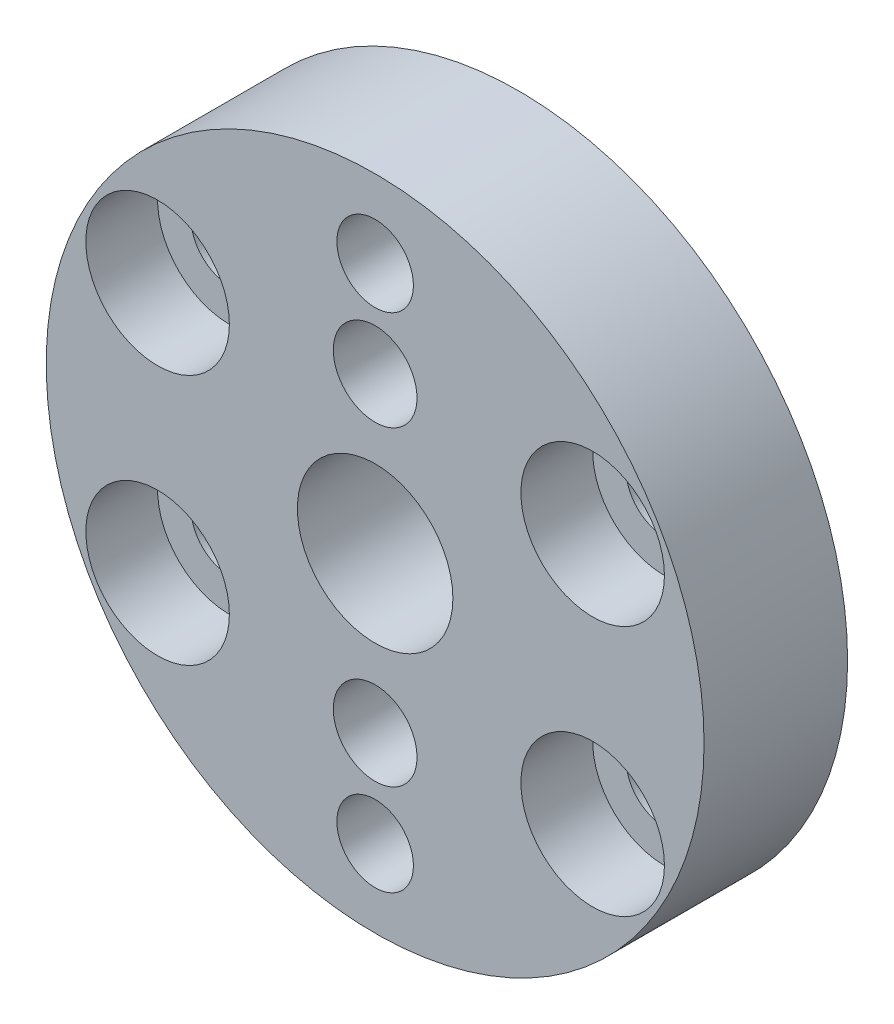
SolidWorks part; units mm, degrees
ref_plane "正面" through (0, 0, 0) normal (0, 0, 1) x (1, 0, 0)
ref_plane "平面" through (0, 0, 0) normal (0, 1, 0) x (1, 0, 0)
ref_plane "右側面" through (0, 0, 0) normal (1, 0, 0) x (0, 0, -1)
sketch "ｽｹｯﾁ1" plane through (0, 0, 0) normal (0, 0, 1) x (1, 0, 0)
  circle A0 centre (0, 0) radius 13.75
  circle A1 centre (0, 0) radius 10.5 construction
  circle A2 centre (0, 10.5) radius 1.6
  circle A3 centre (9.0933, 5.25) radius 1.6
  circle A4 centre (9.0933, -5.25) radius 1.6
  circle A5 centre (0, -10.5) radius 1.6
  circle A6 centre (-9.0933, -5.25) radius 1.6
  circle A7 centre (-9.0933, 5.25) radius 1.6
  circle A8 centre (0, 0) radius 3.25
  point P18 (0, 0)
  dimension "D1" = 27.5
  dimension "D2" = 21
  dimension "D3" = 3.2
  dimension "D5" = 6.5
  dimension "D4" = 6
extrude "ﾎﾞｽ - 押し出し1" add sketch "ｽｹｯﾁ1" along normal blind 6
sketch "ｽｹｯﾁ2" plane through (0, 0, 6) normal (0, 0, 1) x (1, 0, 0)
  line L0 (0, 10.5) -> (0, 0) construction
  line L1 (0, 0) -> (0, 6.5) construction
  circle A0 centre (0, 0) radius 6.5 construction
  circle A1 centre (0, 6.5) radius 1.75
  circle A2 centre (0, -6.5) radius 1.75
  point P11 (0, 0)
  dimension "D1" = 13
  dimension "D2" = 3.5
  dimension "D3" = 0
  dimension "D4" = 2
extrude "ｶｯﾄ - 押し出し1" cut sketch "ｽｹｯﾁ2" against normal through all
sketch "ｽｹｯﾁ3" plane through (0, 0, 6) normal (0, 0, 1) x (1, 0, 0)
  circle A0 centre (9.0933, 5.25) radius 3
  circle A1 centre (-9.0933, -5.25) radius 3
  circle A2 centre (-9.0933, 5.25) radius 3
  circle A3 centre (9.0933, -5.25) radius 3
  dimension "D1" = 6
  dimension "D2" = 6
  dimension "D3" = 6
  dimension "D4" = 6
extrude "ｶｯﾄ - 押し出し2" cut sketch "ｽｹｯﾁ3" against normal blind 3
sketch "ｽｹｯﾁ7" plane through (0, 0, 0) normal (0, 0, -1) x (-1, 0, 0)
  line L1 (1.7527, 3.512) -> (3.464, 6.5239)
  line L2 (3.464, 6.5239) -> (1.7113, 9.5119)
  line L3 (1.7113, 9.5119) -> (-1.7527, 9.488)
  line L4 (-1.7527, 9.488) -> (-3.464, 6.4761)
  line L5 (-3.464, 6.4761) -> (-1.7113, 3.4881)
  line L6 (-1.7113, 3.4881) -> (1.7527, 3.512)
  line L7 (2.3358, -9.0582) -> (3.3833, -5.7563)
  line L8 (3.3833, -5.7563) -> (1.0476, -3.1981)
  line L9 (1.0476, -3.1981) -> (-2.3358, -3.9418)
  line L10 (-2.3358, -3.9418) -> (-3.3833, -7.2437)
  line L11 (-3.3833, -7.2437) -> (-1.0476, -9.8019)
  line L12 (-1.0476, -9.8019) -> (2.3358, -9.0582)
  circle A0 centre (0, 6.5) radius 3 construction
  circle A1 centre (0, -6.5) radius 3 construction
  dimension "D1" = 3
  dimension "D2" = 3
extrude "ｶｯﾄ - 押し出し6" cut sketch "ｽｹｯﾁ7" against normal blind 3
